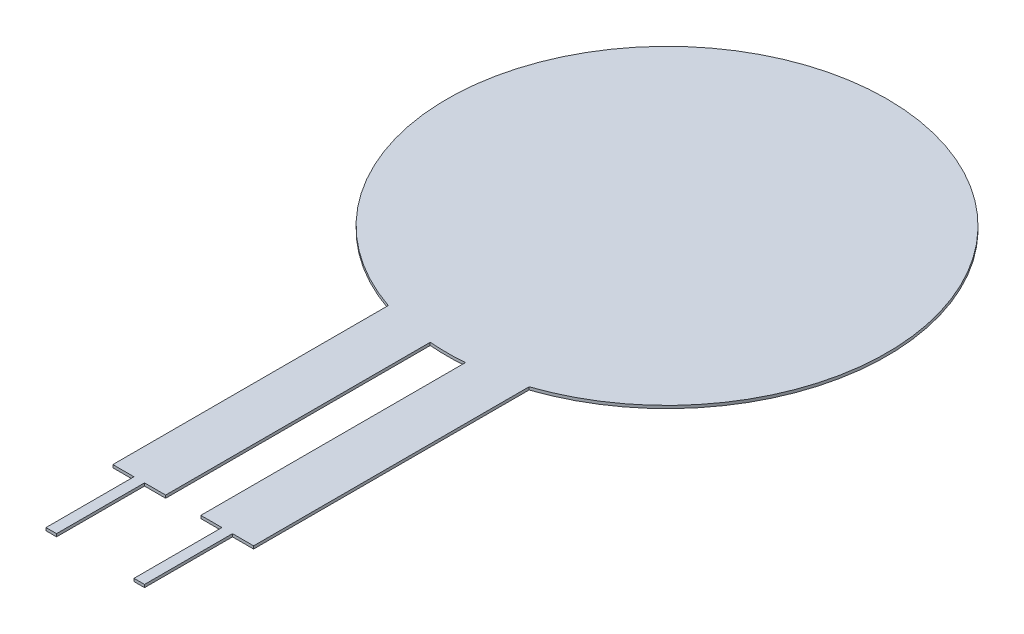
SolidWorks part; units mm, degrees
ref_plane "Front Plane" through (0, 0, 0) normal (0, 0, 1) x (1, 0, 0)
ref_plane "Top Plane" through (0, 0, 0) normal (0, 1, 0) x (1, 0, 0)
ref_plane "Right Plane" through (0, 0, 0) normal (1, 0, 0) x (0, 0, -1)
sketch "Sketch1" plane through (0, 0, 0) normal (0, 1, 0) x (1, 0, 0)
  line L0 (0, 0) -> (0, -15.875) construction
  line L2 (-1.27, -15.8241) -> (-1.27, -34.925)
  line L3 (-1.27, -34.925) -> (-2.794, -34.925)
  line L4 (-5.08, -15.2943) -> (-5.08, -34.925)
  line L5 (-5.08, -15.2943) -> (-5.08, -15.0403)
  line L6 (1.27, -15.8241) -> (1.27, -34.925)
  line L7 (5.08, -15.2943) -> (5.08, -34.925)
  line L8 (5.08, -15.2943) -> (5.08, -15.0403)
  line L10 (1.27, -34.925) -> (2.794, -34.925)
  line L11 (-3.556, -34.925) -> (-5.08, -34.925)
  line L13 (-3.556, -34.925) -> (-3.556, -41.275)
  line L14 (-3.556, -41.275) -> (-2.794, -41.275)
  line L15 (-2.794, -34.925) -> (-2.794, -41.275)
  line L17 (2.794, -34.925) -> (2.794, -41.275)
  line L18 (2.794, -41.275) -> (3.556, -41.275)
  line L19 (3.556, -34.925) -> (3.556, -41.275)
  line L20 (3.556, -34.925) -> (5.08, -34.925)
  arc A0 (-1.27, -15.8241) -> (1.27, -15.8241) centre (0, 0) ccw
  arc A1 (5.08, -15.0403) -> (-5.08, -15.0403) centre (0, 0) ccw
  point P21 (-3.175, -41.275)
  point P22 (-3.175, -35.1014)
  point P23 (3.175, -35.1014)
  point P24 (3.175, -41.275)
  point P25 (0, 15.875)
  point P26 (-4.318, -34.925)
  dimension "D1" = 31.75
  dimension "D2" = 1.27
  dimension "D3" = 3.81
  dimension "D4" = 0.254
  dimension "D5" = 0.762
  dimension "D6" = 0.762
  dimension "D7" = 50.8
  dimension "D8" = 6.35
extrude "Boss-Extrude1" add sketch "Sketch1" along normal blind 0.2032 contours A1 L5 L4 L11 L13 L14 L15 L3 L2 A0 L6 L10 L17 L18 L19 L20 L7 L8
